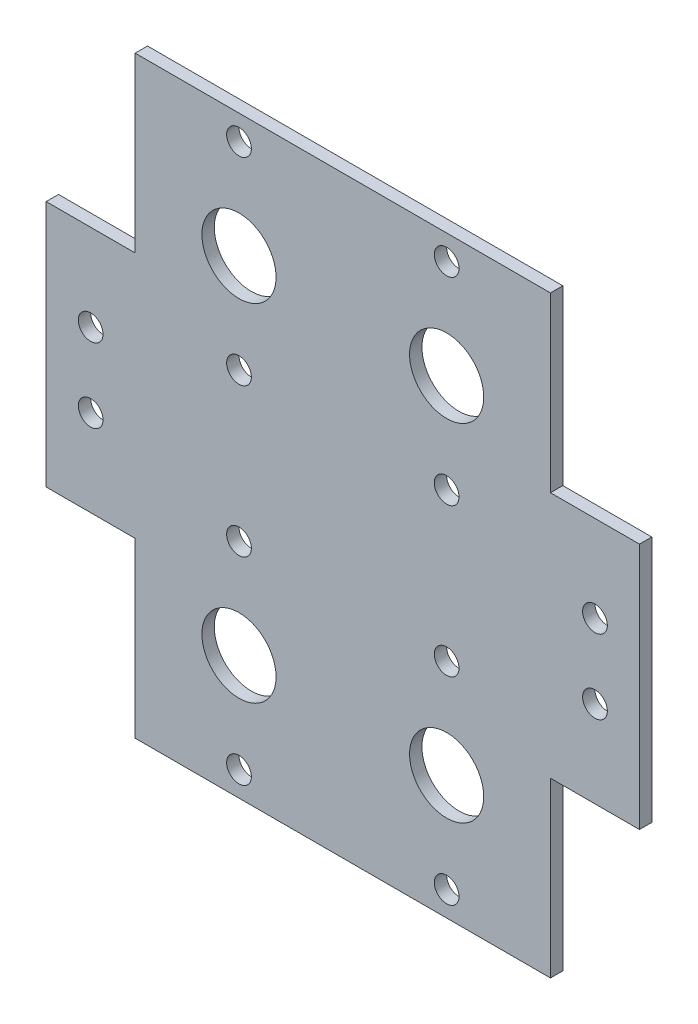
SolidWorks part; units mm, degrees
ref_plane "Front Plane" through (0, 0, 0) normal (0, 0, 1) x (1, 0, 0)
ref_plane "Top Plane" through (0, 0, 0) normal (0, 1, 0) x (1, 0, 0)
ref_plane "Right Plane" through (0, 0, 0) normal (1, 0, 0) x (0, 0, -1)
sketch "Sketch1" plane through (0, 0, 0) normal (0, 0, 1) x (1, 0, 0)
  line L1 (-120, -50) -> (120, -50)
  line L2 (-120, -50) -> (-120, 50)
  line L3 (-120, 50) -> (120, 50)
  line L4 (120, -50) -> (120, 50)
  line L5 (-120, -50) -> (120, 50) construction
  line L6 (-120, 50) -> (120, -50) construction
  point P0 (0, 0)
  dimension "D1" = 240
  dimension "D2" = 100
extrude "Boss-Extrude1" add sketch "Sketch1" along normal blind 5
sketch "Sketch2" plane through (0, 0, 5) normal (0, 0, 1) x (1, 0, 0)
  line L0 (120, 50) -> (-120, 50) construction
  line L1 (-84, -120) -> (84, -120)
  line L2 (-84, -120) -> (-84, 120)
  line L3 (-84, 120) -> (84, 120)
  line L4 (84, -120) -> (84, 120)
  line L5 (-84, -120) -> (84, 120) construction
  line L6 (-84, 120) -> (84, -120) construction
  point P0 (0, 0)
  dimension "D1" = 70
  dimension "D2" = 168
extrude "Boss-Extrude2" add sketch "Sketch2" against normal blind 5
sketch "Sketch3" plane through (0, 0, 5) normal (0, 0, 1) x (1, 0, 0)
  line L0 (-120, 15) -> (120, 15) construction
  line L1 (-120, 50) -> (-120, -50) construction
  line L2 (120, -50) -> (120, 50) construction
  line L3 (-84, 50) -> (-120, 50) construction
  line L4 (-102, 50) -> (-102, -50) construction
  line L5 (-120, -50) -> (-84, -50) construction
  line L6 (-120, 0) -> (0, 0) construction
  line L7 (0, 0) -> (0, 120) construction
  line L8 (84, 120) -> (-84, 120) construction
  circle A0 centre (-102, 15) radius 5
  circle A1 centre (102, 15) radius 5
  circle A2 centre (102, -15) radius 5
  circle A3 centre (-102, -15) radius 5
  dimension "D2" = 10
  dimension "D1" = 35
extrude "Cut-Extrude1" cut sketch "Sketch3" against normal blind 5
sketch "Sketch4" plane through (0, 0, 5) normal (0, 0, 1) x (1, 0, 0)
  line L0 (0, 120) -> (0, -120) construction
  line L1 (84, 120) -> (-84, 120) construction
  line L2 (-84, -120) -> (84, -120) construction
  line L3 (-84, -70) -> (0, -70) construction
  line L4 (-84, -50) -> (-84, -120) construction
  line L5 (-42, -30) -> (-42, -110) construction
  line L6 (42, -30) -> (42, -110) construction
  line L7 (-120, 0) -> (120, 0) construction
  line L8 (-120, 50) -> (-120, -50) construction
  line L9 (120, -50) -> (120, 50) construction
  line L10 (42, 30) -> (42, 110) construction
  line L11 (-42, 30) -> (-42, 110) construction
  line L12 (-84, 70) -> (0, 70) construction
  circle A0 centre (-42, -70) radius 15
  circle A1 centre (42, -70) radius 15
  circle A2 centre (-42, -30) radius 5
  circle A3 centre (-42, -110) radius 5
  circle A4 centre (42, -110) radius 5
  circle A5 centre (42, -30) radius 5
  circle A6 centre (42, 30) radius 5
  circle A7 centre (42, 110) radius 5
  circle A8 centre (-42, 110) radius 5
  circle A9 centre (-42, 30) radius 5
  circle A10 centre (42, 70) radius 15
  circle A11 centre (-42, 70) radius 15
  dimension "D1" = 30
  dimension "D3" = 10
  dimension "D2" = 50
  dimension "D4" = 80
  dimension "D5" = 40
extrude "Cut-Extrude2" cut sketch "Sketch4" against normal blind 5
